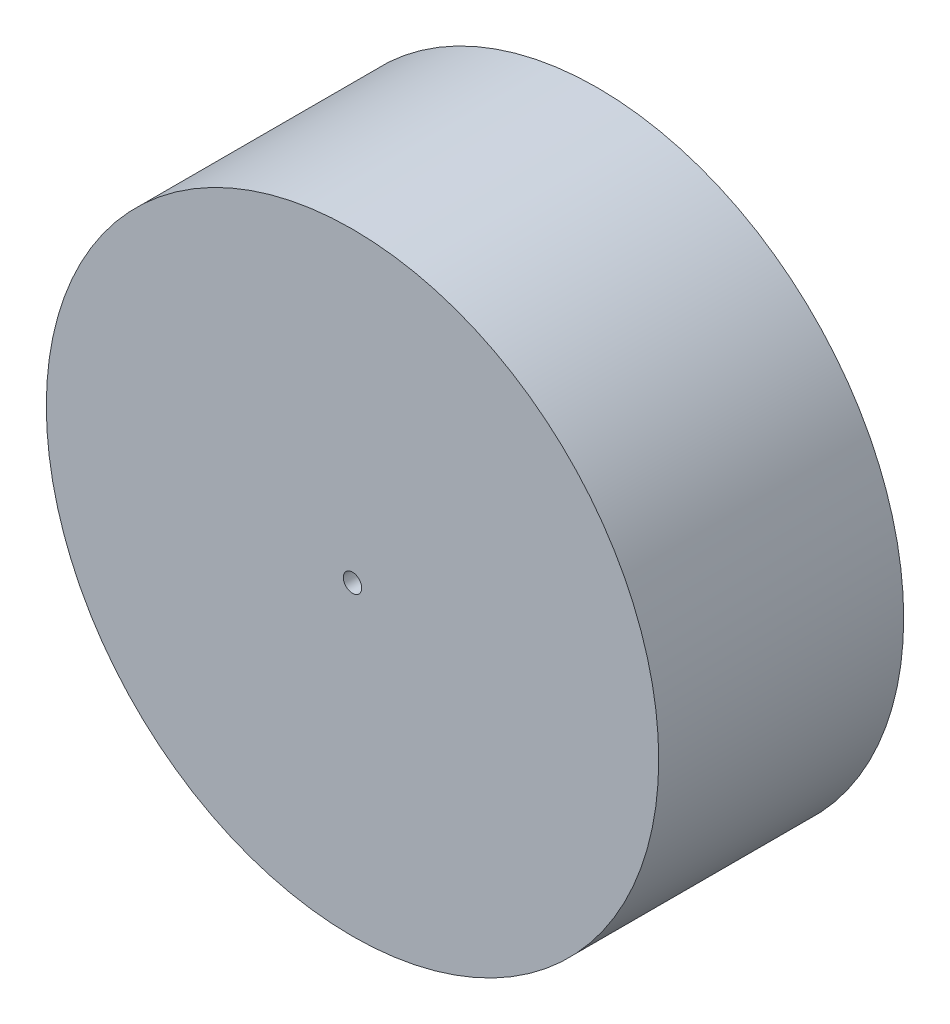
SolidWorks part; units mm, degrees
ref_plane "Front Plane" through (0, 0, 0) normal (0, 0, 1) x (1, 0, 0)
ref_plane "Top Plane" through (0, 0, 0) normal (0, 1, 0) x (1, 0, 0)
ref_plane "Right Plane" through (0, 0, 0) normal (1, 0, 0) x (0, 0, -1)
sketch "Sketch1" plane through (0, 0, 0) normal (0, 0, 1) x (1, 0, 0)
  circle A0 centre (0, 0) radius 50
  dimension "D1" = 100
extrude "Boss-Extrude1" add sketch "Sketch1" along normal blind 40
sketch "Sketch2" plane through (0, 0, 0) normal (0, 0, -1) x (-1, 0, 0)
  circle A0 centre (0, 0) radius 30
  dimension "D1" = 60
extrude "Cut-Extrude1" cut sketch "Sketch2" against normal blind 25
sketch "Sketch3" plane through (0, 0, 25) normal (0, 0, -1) x (-1, 0, 0)
  line L1 (4.0828, -4.3967) -> (5.849, 1.3374)
  line L2 (5.849, 1.3374) -> (1.7663, 5.7341)
  line L3 (1.7663, 5.7341) -> (-4.0828, 4.3967)
  line L4 (-4.0828, 4.3967) -> (-5.849, -1.3374)
  line L5 (-5.849, -1.3374) -> (-1.7663, -5.7341)
  line L6 (-1.7663, -5.7341) -> (4.0828, -4.3967)
  circle A0 centre (0, 0) radius 5.1962 construction
  dimension "D1" = 6
extrude "Cut-Extrude2" cut sketch "Sketch3" against normal blind 5
sketch "Sketch5" plane through (0, 0, 40) normal (0, 0, 1) x (1, 0, 0)
  circle A0 centre (0, 0) radius 1.5
  dimension "D1" = 3
extrude "Cut-Extrude3" cut sketch "Sketch5" against normal blind 40
